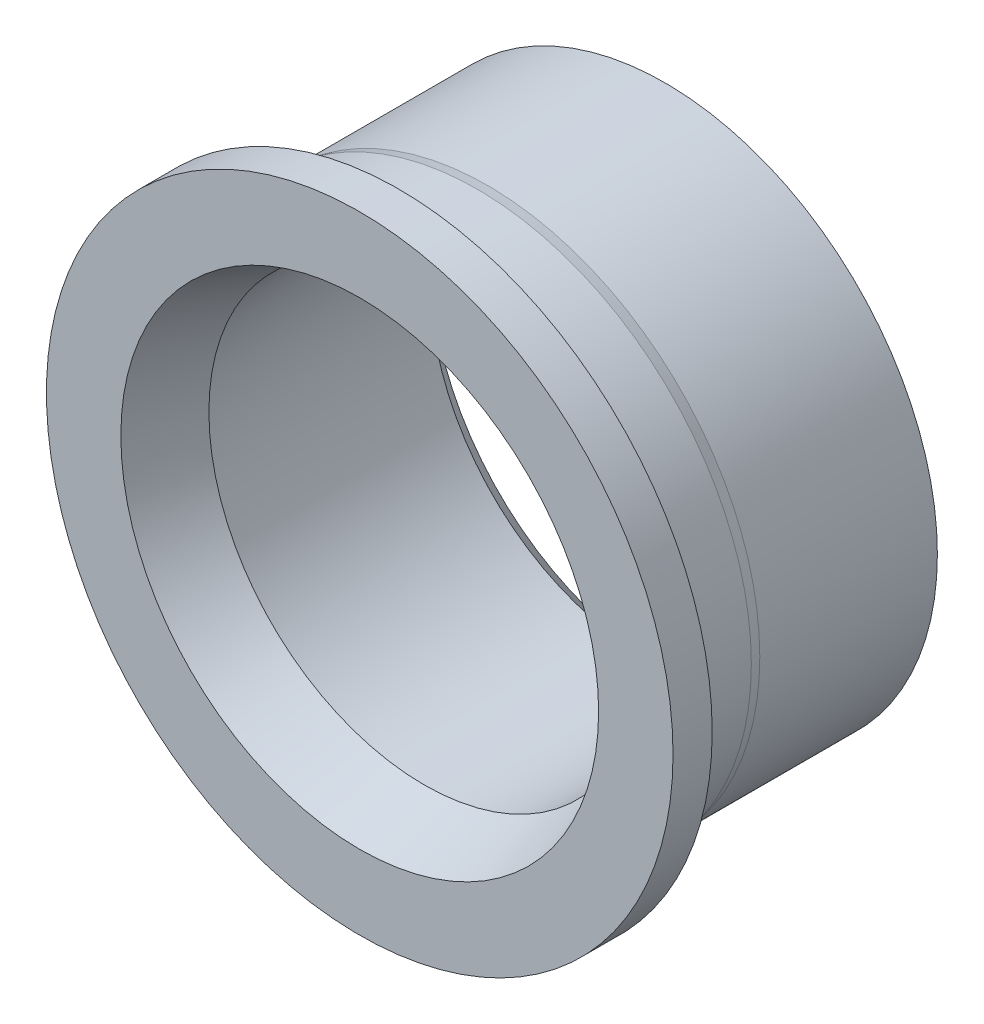
SolidWorks part; units mm, degrees
material "PA Тип 6"
ref_plane "Спереди" through (0, 0, 0) normal (0, 0, 1) x (1, 0, 0)
ref_plane "Сверху" through (0, 0, 0) normal (0, 1, 0) x (1, 0, 0)
ref_plane "Справа" through (0, 0, 0) normal (1, 0, 0) x (0, 0, -1)
sketch "Эскиз1" plane through (0, 0, 0) normal (1, 0, 0) x (0, 0, -1)
  line L0 (0, 5.5) -> (7.8, 5.5)
  line L1 (7.8, 5.5) -> (7.8, 6.95)
  line L2 (1, 7) -> (3, 7)
  line L3 (1, 7) -> (1, 8)
  line L4 (1, 8) -> (0, 8)
  line L5 (0, 8) -> (0, 5.5)
  line L6 (0, 0) -> (9.7337, 0) construction
  line L7 (3, 7) -> (3.2656, 6.95)
  line L8 (3.2656, 6.95) -> (7.8, 6.95)
  dimension "D1" = 11
  dimension "D2" = 2
  dimension "D3" = 16
  dimension "D4" = 7.8
  dimension "D5" = 6.8
  dimension "D6" = 14
  dimension "D7" = 13.9
revolve "Повернуть1" add sketch "Эскиз1" angle 360 about L6
chamfer "Фаска1" distance 0.5 angle 45 1 edges at (5.5, 0, -7.8)
chamfer "Фаска2" distance 0.6 angle 70 1 edges at (5.5, 0, 0)
